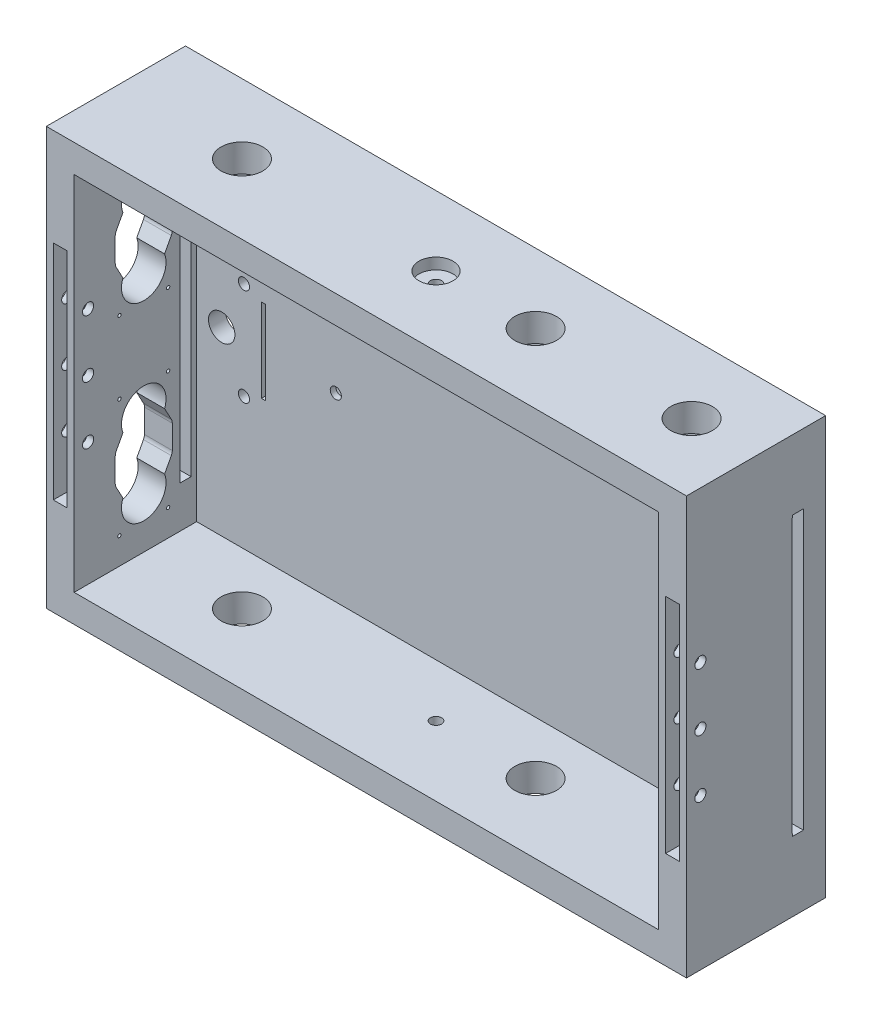
SolidWorks part; units mm, degrees
ref_plane "Front Plane" through (0, 0, 0) normal (0, 0, 1) x (1, 0, 0)
ref_plane "Top Plane" through (0, 0, 0) normal (0, 1, 0) x (1, 0, 0)
ref_plane "Right Plane" through (0, 0, 0) normal (1, 0, 0) x (0, 0, -1)
sketch "Sketch1" plane through (0, 0, 0) normal (0, 1, 0) x (1, 0, 0)
  line L1 (0, 0) -> (230, 0)
  line L2 (0, 0) -> (0, 50)
  line L3 (0, 50) -> (230, 50)
  line L4 (230, 0) -> (230, 50)
  dimension "D1" = 230
  dimension "D2" = 50
extrude "Boss-Extrude1" add sketch "Sketch1" along normal blind 150
sketch "Sketch2" plane through (0, 0, 0) normal (0, 0, 1) x (1, 0, 0)
  line L0 (0, 150) -> (0, 0) construction
  line L1 (10, 140) -> (220, 140)
  line L2 (10, 140) -> (10, 10)
  line L3 (10, 10) -> (220, 10)
  line L4 (220, 140) -> (220, 10)
  line L5 (0, 150) -> (230, 150) construction
  line L6 (0, 0) -> (230, 0) construction
  line L7 (230, 150) -> (230, 0) construction
  dimension "D1" = 10
  dimension "D2" = 10
  dimension "D3" = 10
  dimension "D4" = 10
extrude "Cut-Extrude1" cut sketch "Sketch2" against normal blind 44
sketch "Sketch3" plane through (0, 150, 0) normal (0, 1, 0) x (1, 0, 0)
  line L0 (0, 25) -> (230, 25) construction
  line L1 (0, 50) -> (0, 0) construction
  line L2 (230, 0) -> (230, 50) construction
  line L3 (115, 50) -> (115, 0) construction
  line L4 (230, 50) -> (0, 50) construction
  line L5 (0, 0) -> (230, 0) construction
  circle A0 centre (115, 25) radius 6.125
extrude "Cut-Extrude2" cut sketch "Sketch3" against normal blind 4
sketch "Sketch4" plane through (0, 0, 0) normal (0, 1, 0) x (1, 0, 0)
  line L0 (230, 25) -> (0, 25) construction
  line L1 (230, 0) -> (230, 50) construction
  line L2 (0, 50) -> (0, 0) construction
  circle A0 centre (115, 25) radius 6.125
extrude "Cut-Extrude4" cut sketch "Sketch4" along normal blind 4
sketch "Sketch5" plane through (0, 0, -50) normal (0, 0, -1) x (-1, 0, 0)
  line L0 (0, 75) -> (-230, 75) construction
  line L1 (0, 150) -> (0, 0) construction
  line L2 (-230, 150) -> (-230, 0) construction
  line L3 (-115, 150) -> (-115, 0) construction
  line L4 (-230, 150) -> (0, 150) construction
  line L5 (-230, 0) -> (0, 0) construction
  line L6 (-230, 75) -> (-170, 75) construction
  circle A2 centre (-60, 75) radius 6.125
  dimension "D1" = 60
extrude "Cut-Extrude5" cut sketch "Sketch5" against normal blind 4
sketch "Sketch7" plane through (0, 0, -46) normal (0, 0, -1) x (-1, 0, 0)
  circle A0 centre (-60, 75) radius 2
extrude "Cut-Extrude7" cut sketch "Sketch7" against normal through all
sketch "Sketch8" plane through (0, 146, 0) normal (0, 1, 0) x (1, 0, 0)
  circle A0 centre (115, 25) radius 2
extrude "Cut-Extrude8" cut sketch "Sketch8" against normal through all
sketch "Sketch10" plane through (0, 0, -50) normal (0, 0, -1) x (-1, 0, 0)
  line L0 (0, 75) -> (-230, 75) construction
  line L1 (0, 150) -> (0, 0) construction
  line L2 (-230, 150) -> (-230, 0) construction
  line L3 (-115, 150) -> (-115, 0) construction
  line L4 (-230, 150) -> (0, 150) construction
  line L5 (-230, 0) -> (0, 0) construction
  line L6 (0, 75) -> (-27, 75) construction
  line L7 (-27, 75) -> (-27, 96) construction
  line L8 (-27, 75) -> (-27, 54) construction
  line L9 (-27, 96) -> (-27, 92.5) construction
  line L10 (-27, 75) -> (-19, 75) construction
  line L11 (-27, 75) -> (-19, 75) construction
  line L12 (-34.7684, 60) -> (-33.2684, 60)
  line L14 (-34.7684, 60) -> (-34.7684, 90)
  line L15 (-34.7684, 90) -> (-33.2684, 90)
  line L16 (-33.2684, 60) -> (-33.2684, 90)
  circle A0 centre (-27, 92.5) radius 2
  circle A1 centre (-27, 57.5) radius 2
  circle A2 centre (-19, 75) radius 4.75
  point P24 (-34.7684, 75)
  point P27 (-33.2684, 75)
  dimension "D1" = 21
  dimension "D2" = 9.5
  dimension "D3" = 8
  dimension "D4" = 35
  dimension "D5" = 30
extrude "Cut-Extrude9" cut sketch "Sketch10" against normal up to next
sketch "Sketch11" plane through (0, 150, 0) normal (0, 1, 0) x (1, 0, 0)
  line L0 (0, 25) -> (230, 25) construction
  line L1 (0, 50) -> (0, 0) construction
  line L2 (230, 0) -> (230, 50) construction
  circle A3 centre (45.2802, 25) radius 7.5
  circle A4 centre (150.7816, 25) radius 7.5
  circle A5 centre (206.8207, 25) radius 7.5
  dimension "D1" = 15
extrude "Cut-Extrude10" cut sketch "Sketch11" against normal through all
sketch "Sketch13" plane through (0, 0, 0) normal (-1, 0, 0) x (0, 0, 1)
  line L0 (-25, 0) -> (-25, 150) construction
  line L1 (-50, 0) -> (0, 0) construction
  line L2 (-50, 150) -> (0, 150) construction
  line L3 (0, 75) -> (-50, 75) construction
  line L4 (0, 150) -> (0, 0) construction
  line L5 (-50, 150) -> (-50, 0) construction
  line L6 (-25, 75) -> (-25, 50.75) construction
  line B0 (-36.75, 40.75) -> (-13.25, 40.75) construction
  line B1 (-13.25, 16.5) -> (-13.25, 65)
  line B2 (-13.25, 16.5) -> (-36.75, 16.5)
  line B3 (-36.75, 16.5) -> (-36.75, 65)
  line B4 (-13.25, 65) -> (-36.75, 65)
  line B5 (-25, 16.5) -> (-25, 27.75) construction
  line B6 (-25, 16.5) -> (-25, 27.75) construction
  line B7 (-36.75, 40.75) -> (-35.25, 40.75) construction
  line B8 (-35.25, 44.998) -> (-35.25, 36.502)
  line B9 (-13.25, 40.75) -> (-14.75, 40.75) construction
  line B10 (-14.75, 44.998) -> (-14.75, 36.502)
  line B11 (-25, 27.75) -> (-33, 27.75) construction
  line B12 (-15.1048, 46.4131) -> (-17.5167, 50.9216)
  line B13 (-34.8952, 46.4131) -> (-32.4833, 50.9216)
  line B14 (-25, 27.75) -> (-17, 27.75) construction
  line B15 (-25, 27.75) -> (-19.3431, 33.4069) construction
  line B16 (-25, 27.75) -> (-32.4833, 30.5784) construction
  line B17 (-25, 27.75) -> (-17.5167, 30.5784) construction
  line B18 (-34.8952, 35.0869) -> (-32.4833, 30.5784)
  line B19 (-15.1048, 35.0869) -> (-17.5167, 30.5784)
  arc B20 (-32.4833, 30.5784) -> (-17.5167, 30.5784) centre (-25, 27.75) ccw
  circle B21 centre (-33.75, 19.5) radius 0.6
  arc B22 (-34.8952, 35.0869) -> (-35.25, 36.502) centre (-32.25, 36.502) cw
  arc B23 (-14.75, 36.502) -> (-15.1048, 35.0869) centre (-17.75, 36.502) cw
  circle B24 centre (-16.25, 19.5) radius 0.6
  arc B25 (-14.75, 44.998) -> (-15.1048, 46.4131) centre (-17.75, 44.998) ccw
  circle B26 centre (-16.25, 62) radius 0.6
  arc B27 (-34.8952, 46.4131) -> (-35.25, 44.998) centre (-32.25, 44.998) ccw
  arc B28 (-32.4833, 50.9216) -> (-17.5167, 50.9216) centre (-25, 53.75) cw
  circle B29 centre (-33.75, 62) radius 0.6
  dimension "D1" = 10
sketch_block_instance "Block1-1"
sketch_block "Block1" parameters "D3"=3, "D4"=3, "D1"=23.5, "D2"=3
sketch "Sketch14" plane through (0, 0, 0) normal (-1, 0, 0) x (0, 0, 1)
  line L4 (-35.25, 44.998) -> (-35.25, 36.502) construction
  line L5 (-34.8952, 35.0869) -> (-32.4833, 30.5784) construction
  line L6 (-15.1048, 35.0869) -> (-17.5167, 30.5784) construction
  line L7 (-14.75, 44.998) -> (-14.75, 36.502) construction
  line L8 (-15.1048, 46.4131) -> (-17.5167, 50.9216) construction
  line L9 (-34.8952, 46.4131) -> (-32.4833, 50.9216) construction
  line L14 (-35.25, 44.998) -> (-35.25, 36.502)
  line L15 (-34.8952, 35.0869) -> (-32.4833, 30.5784)
  line L16 (-15.1048, 35.0869) -> (-17.5167, 30.5784)
  line L17 (-14.75, 44.998) -> (-14.75, 36.502)
  line L18 (-15.1048, 46.4131) -> (-17.5167, 50.9216)
  line L19 (-34.8952, 46.4131) -> (-32.4833, 50.9216)
  line L20 (0, 75) -> (-50, 75) construction
  line L21 (0, 150) -> (0, 0) construction
  line L22 (-50, 150) -> (-50, 0) construction
  line L23 (-34.8952, 103.5869) -> (-32.4833, 99.0784)
  line L24 (-15.1048, 103.5869) -> (-17.5167, 99.0784)
  line L25 (-14.75, 105.002) -> (-14.75, 113.498)
  line L26 (-15.1048, 114.9131) -> (-17.5167, 119.4216)
  line L27 (-34.8952, 114.9131) -> (-32.4833, 119.4216)
  line L28 (-35.25, 105.002) -> (-35.25, 113.498)
  circle A2 centre (-33.75, 62) radius 0.6 construction
  arc A4 (-35.25, 36.502) -> (-34.8952, 35.0869) centre (-32.25, 36.502) ccw construction
  arc A5 (-32.4833, 30.5784) -> (-17.5167, 30.5784) centre (-25, 27.75) ccw construction
  arc A6 (-15.1048, 35.0869) -> (-14.75, 36.502) centre (-17.75, 36.502) ccw construction
  arc A7 (-14.75, 44.998) -> (-15.1048, 46.4131) centre (-17.75, 44.998) ccw construction
  arc A8 (-17.5167, 50.9216) -> (-32.4833, 50.9216) centre (-25, 53.75) ccw construction
  arc A9 (-34.8952, 46.4131) -> (-35.25, 44.998) centre (-32.25, 44.998) ccw construction
  circle A12 centre (-33.75, 62) radius 0.6
  arc A14 (-35.25, 36.502) -> (-34.8952, 35.0869) centre (-32.25, 36.502) ccw
  arc A15 (-32.4833, 30.5784) -> (-17.5167, 30.5784) centre (-25, 27.75) ccw
  arc A16 (-15.1048, 35.0869) -> (-14.75, 36.502) centre (-17.75, 36.502) ccw
  arc A17 (-14.75, 44.998) -> (-15.1048, 46.4131) centre (-17.75, 44.998) ccw
  arc A18 (-17.5167, 50.9216) -> (-32.4833, 50.9216) centre (-25, 53.75) ccw
  arc A19 (-34.8952, 46.4131) -> (-35.25, 44.998) centre (-32.25, 44.998) ccw
  circle A20 centre (-16.25, 19.5) radius 0.6 construction
  circle A21 centre (-16.25, 19.5) radius 0.6
  circle A22 centre (-16.25, 62) radius 0.6 construction
  circle A23 centre (-33.75, 19.5) radius 0.6 construction
  circle A24 centre (-16.25, 62) radius 0.6
  circle A25 centre (-33.75, 19.5) radius 0.6
  circle A26 centre (-33.75, 130.5) radius 0.6
  circle A27 centre (-16.25, 88) radius 0.6
  circle A28 centre (-16.25, 130.5) radius 0.6
  arc A29 (-34.8952, 103.5869) -> (-35.25, 105.002) centre (-32.25, 105.002) cw
  arc A30 (-17.5167, 99.0784) -> (-32.4833, 99.0784) centre (-25, 96.25) cw
  arc A31 (-14.75, 105.002) -> (-15.1048, 103.5869) centre (-17.75, 105.002) cw
  arc A32 (-15.1048, 114.9131) -> (-14.75, 113.498) centre (-17.75, 113.498) cw
  arc A33 (-32.4833, 119.4216) -> (-17.5167, 119.4216) centre (-25, 122.25) cw
  arc A34 (-35.25, 113.498) -> (-34.8952, 114.9131) centre (-32.25, 113.498) cw
  circle A35 centre (-33.75, 88) radius 0.6
extrude "Cut-Extrude12" cut sketch "Sketch14" against normal up to next
sketch "Sketch15" plane through (0, 0, 0) normal (0, 0, 1) x (1, 0, 0)
  line L5 (5, 140) -> (5, 10) construction
  line L6 (5, 75) -> (0, 75) construction
  line L7 (7.5, 115) -> (2.5, 115)
  line L10 (7.5, 35) -> (2.5, 35)
  line L11 (2.5, 115) -> (2.5, 35)
  line L12 (7.5, 115) -> (7.5, 35)
  line L13 (10, 140) -> (0, 140) construction
  line L14 (0, 150) -> (0, 0) construction
  line L15 (10, 10) -> (0, 10) construction
  point P12 (5, 115)
  dimension "D1" = 80
  dimension "D2" = 65
  dimension "D3" = 65
extrude "Cut-Extrude13" cut sketch "Sketch15" against normal blind 10
sketch "Sketch16" plane through (0, 0, 0) normal (-1, 0, 0) x (0, 0, 1)
  line L0 (-5, 75) -> (-5, 35) construction
  line L1 (-5, 75) -> (-10, 75) construction
  circle A0 centre (-5, 54.2758) radius 2
  circle A1 centre (-5, 75) radius 2
  circle A2 centre (-5, 95.7242) radius 2
extrude "Cut-Extrude14" cut sketch "Sketch16" against normal through all
sketch "Sketch17" plane through (0, 0, 0) normal (-1, 0, 0) x (0, 0, 1)
  line L0 (-50, 150) -> (0, 150) construction
  line L5 (-42, 0) -> (-42, 150) construction
  line L6 (-42, 0) -> (-42, 25) construction
  line L7 (-42, 25) -> (-46, 25) construction
  line L9 (-42, 75) -> (-33.8804, 75) construction
  line L10 (-38, 25) -> (-37.9402, 75)
  line L13 (-38, 125) -> (-37.9402, 75)
  line L14 (-38, 25) -> (-42, 25)
  line L15 (-42, 25) -> (-42, 125)
  line L16 (-42, 125) -> (-38, 125)
  point P12 (-46, 75)
extrude "Cut-Extrude15" cut sketch "Sketch17" against normal through all
ref_plane "Plane1" through (115, 0, 0) normal (1, 0, 0) x (0, 0, -1)
mirror "Mirror1" about plane through (115, 0, 0) normal (1, 0, 0) of "Cut-Extrude13"
